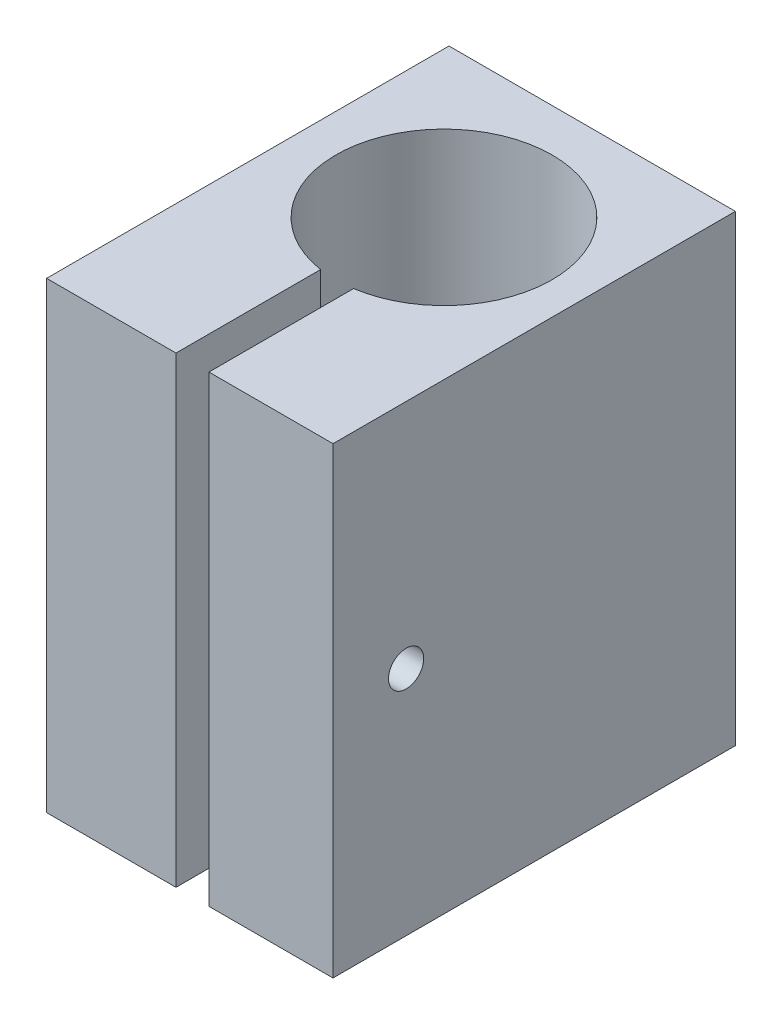
SolidWorks part; units mm, degrees
ref_plane "Спереди" through (0, 0, 0) normal (0, 0, 1) x (1, 0, 0)
ref_plane "Сверху" through (0, 0, 0) normal (0, 1, 0) x (1, 0, 0)
ref_plane "Справа" through (0, 0, 0) normal (1, 0, 0) x (0, 0, -1)
sketch "Эскиз1" plane through (0, 0, 0) normal (0, 1, 0) x (1, 0, 0)
  line L1 (-14.235, 20) -> (14.235, 20)
  line L2 (-14.235, 20) -> (-14.235, -20)
  line L3 (-14.235, -20) -> (-1.3731, -20)
  line L4 (14.235, 20) -> (14.235, -20)
  line L5 (-14.235, 20) -> (14.235, -20) construction
  line L6 (-14.235, -20) -> (14.235, 20) construction
  line L7 (-39.5805, 5) -> (37.2286, 5) construction
  line L8 (-1.3731, -20) -> (-1.3731, -5.6245)
  line L9 (1.9031, -20) -> (1.9031, -5.6245)
  line L10 (1.9031, -20) -> (14.235, -20)
  arc A0 (1.9031, -5.6245) -> (-1.3731, -5.6245) centre (0.265, 5) ccw
  point P0 (0, 0)
  dimension "D5" = 21.5
  dimension "D3" = 13.97
  dimension "D1" = 28.47
  dimension "D2" = 40
  dimension "D4" = 15
extrude "Бобышка-Вытянуть1" add sketch "Эскиз1" along normal blind 46
sketch "Эскиз2" plane through (-14.235, 0, 0) normal (-1, 0, 0) x (0, 0, 1)
  line L0 (12.733, 46) -> (12.733, 0) construction
  line L1 (-20, 46) -> (20, 46) construction
  line L2 (-20, 0) -> (20, 0) construction
  line L3 (33.1578, 23) -> (-23.6542, 23) construction
  line L11 (12.733, 19.75) -> (15.5476, 21.375)
  line L12 (15.5476, 21.375) -> (15.5476, 24.625)
  line L13 (15.5476, 24.625) -> (12.733, 26.25)
  line L14 (12.733, 26.25) -> (9.9184, 24.625)
  line L15 (9.9184, 24.625) -> (9.9184, 21.375)
  line L16 (9.9184, 21.375) -> (12.733, 19.75)
  circle A0 centre (12.733, 23) radius 3.25 construction
  dimension "D1" = 6.5
extrude "Вырез-Вытянуть1" cut sketch "Эскиз2" against normal blind 3
sketch "Эскиз3" plane through (-11.235, 0, 0) normal (-1, 0, 0) x (0, 0, 1)
  line L0 (12.733, 26.25) -> (12.733, 19.75) construction
  line L1 (12.733, 19.75) -> (15.5476, 21.375) construction
  circle A2 centre (12.733, 23) radius 1.75
  dimension "D1" = 3.5
extrude "Вырез-Вытянуть2" cut sketch "Эскиз3" against normal through all
